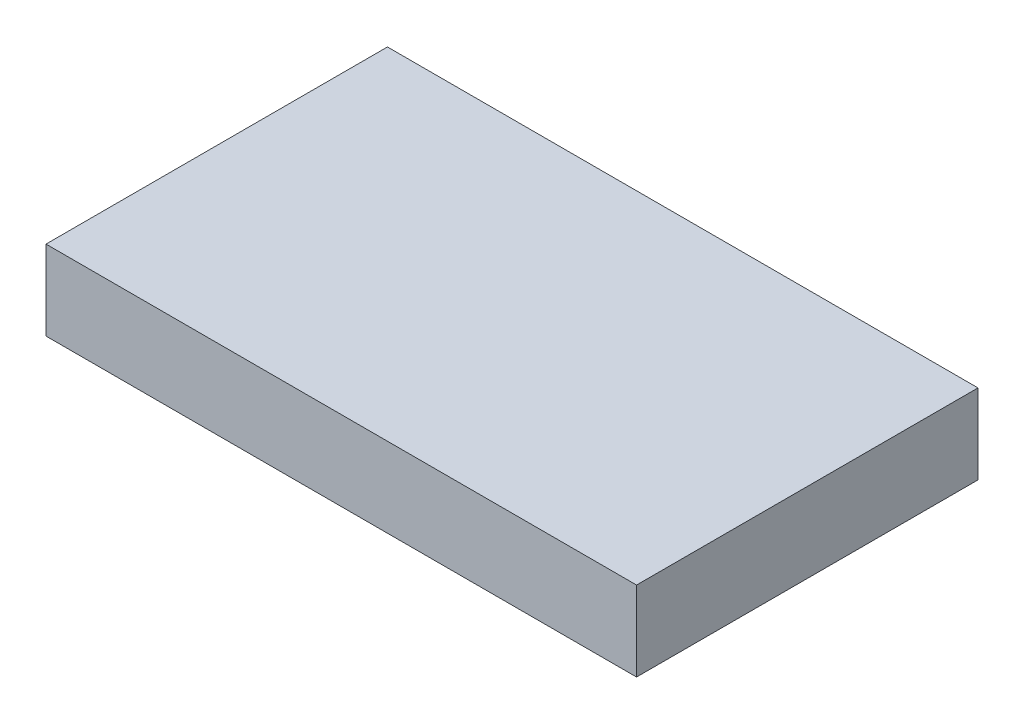
SolidWorks part; units mm, degrees
ref_plane "Front Plane" through (0, 0, 0) normal (0, 0, 1) x (1, 0, 0)
ref_plane "Top Plane" through (0, 0, 0) normal (0, 1, 0) x (1, 0, 0)
ref_plane "Right Plane" through (0, 0, 0) normal (1, 0, 0) x (0, 0, -1)
sketch "Sketch1" plane through (0, 0, 0) normal (0, 1, 0) x (1, 0, 0)
  line L1 (-31.3963, -7.0362) -> (49.3757, -7.0362)
  line L2 (-31.3963, -7.0362) -> (-31.3963, -53.7362)
  line L3 (-31.3963, -53.7362) -> (49.3757, -53.7362)
  line L4 (49.3757, -7.0362) -> (49.3757, -53.7362)
  dimension "D1" = 80.772
  dimension "D2" = 46.7
extrude "Boss-Extrude1" add sketch "Sketch1" along normal blind 10.9
sketch "Sketch2" plane through (0, 10.9, 0) normal (0, 1, 0) x (1, 0, 0)
  line L0 (-31.3963, -46.66) -> (-26.0963, -46.66) construction
  line L1 (-31.3963, -7.0362) -> (-31.3963, -53.7362) construction
  line L2 (-26.0963, -7.0362) -> (-26.0963, -53.7362) construction
  line L3 (49.3757, -7.0362) -> (-31.3963, -7.0362) construction
  line L4 (-31.3963, -53.7362) -> (49.3757, -53.7362) construction
  line L5 (49.3757, -46.66) -> (44.0757, -46.66) construction
  line L6 (49.3757, -53.7362) -> (49.3757, -7.0362) construction
  line L7 (44.0757, -7.0362) -> (44.0757, -53.7362) construction
  line L8 (-26.0963, -7.0362) -> (-26.0963, -22.7362)
  line L9 (44.0757, -7.0362) -> (44.0757, -22.7362) construction
  line L10 (-26.0963, -53.7362) -> (-26.0963, -38.7362)
  line L11 (44.0757, -53.7362) -> (44.0757, -38.7362)
  dimension "D1" = 5.3
